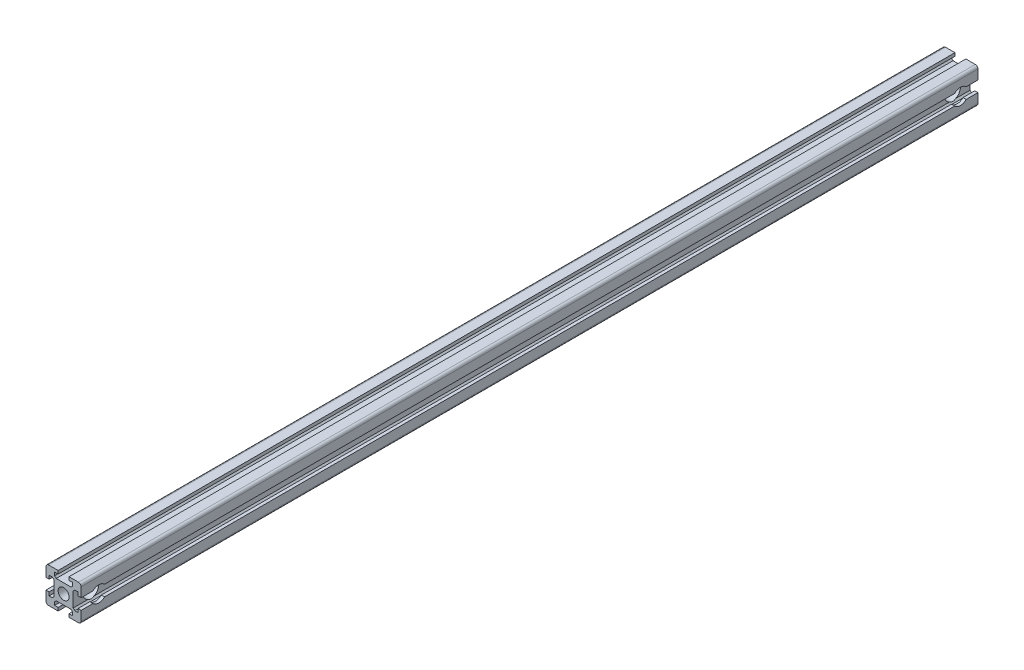
SolidWorks part; units mm, degrees
material "6061 Alloy"
ref_plane "Front Plane" through (0, 0, 0) normal (0, 0, 1) x (1, 0, 0)
ref_plane "Top Plane" through (0, 0, 0) normal (0, 1, 0) x (1, 0, 0)
ref_plane "Right Plane" through (0, 0, 0) normal (1, 0, 0) x (0, 0, -1)
sketch "Sketch1" plane through (0, 0, 0) normal (0, 0, 1) x (1, 0, 0)
  line L0 (-10, 3.1) -> (-8.2, 3.1)
  line L1 (-8.5, 10) -> (-3.1, 10) construction
  line L2 (-10, 8.5) -> (-10, 3.1) construction
  line L3 (-10, -3.1) -> (-10, -8.5) construction
  line L4 (-8.5, -10) -> (-3.1, -10) construction
  line L5 (-10, -3.1) -> (-10, -8.5)
  line L6 (-8.5, -10) -> (-3.1, -10)
  line L7 (-8.2, 3.1) -> (-8.2, 5.1)
  line L8 (-8.2, 5.1) -> (-6.4, 5.1)
  line L9 (-10, -3.1) -> (-8.2, -3.1)
  line L10 (-8.2, -3.1) -> (-8.2, -5.1)
  line L11 (-8.2, -5.1) -> (-6.4, -5.1)
  line L13 (-6.4, 5.1) -> (-5.4929, 4.1929)
  line L14 (-5.4929, 4.1929) -> (-5.4929, -4.1929)
  line L15 (-6.4, -5.1) -> (-5.4929, -4.1929)
  line L16 (-3.1, 10) -> (-3.1, 8.2)
  line L17 (-3.1, 8.2) -> (-5.1, 8.2)
  line L19 (-5.1, 8.2) -> (-5.1, 6.4)
  line L20 (-5.1, 6.4) -> (-4.1929, 5.4929)
  line L21 (-4.1929, 5.4929) -> (4.1929, 5.4929)
  line L22 (4.1929, 5.4929) -> (5.1, 6.4)
  line L23 (5.1, 6.4) -> (5.1, 8.2)
  line L24 (5.1, 8.2) -> (3.1, 8.2)
  line L25 (3.1, 8.2) -> (3.1, 10)
  line L26 (-3.1, -10) -> (-3.1, -8.2)
  line L27 (-3.1, -8.2) -> (-5.1, -8.2)
  line L28 (-5.1, -8.2) -> (-5.1, -6.4)
  line L29 (-5.1, -6.4) -> (-4.1929, -5.4929)
  line L30 (-4.1929, -5.4929) -> (4.1929, -5.4929)
  line L31 (4.1929, -5.4929) -> (5.1, -6.4)
  line L32 (5.1, -6.4) -> (5.1, -8.2)
  line L33 (5.1, -8.2) -> (3.1, -8.2)
  line L34 (3.1, -8.2) -> (3.1, -10)
  line L35 (3.1, -10) -> (8.5, -10)
  line L36 (10, -8.5) -> (10, -3.1)
  line L37 (10, -3.1) -> (8.2, -3.1)
  line L38 (8.2, -3.1) -> (8.2, -5.1)
  line L39 (8.2, -5.1) -> (6.4, -5.1)
  line L40 (6.4, -5.1) -> (5.4929, -4.1929)
  line L41 (5.4929, -4.1929) -> (5.4929, 4.1929)
  line L42 (5.4929, 4.1929) -> (6.4, 5.1)
  line L43 (6.4, 5.1) -> (8.2, 5.1)
  line L44 (8.2, 5.1) -> (8.2, 3.1)
  line L45 (8.2, 3.1) -> (10, 3.1)
  line L46 (10, 3.1) -> (10, 8.5)
  line L47 (8.5, 10) -> (3.1, 10)
  line L48 (-3.1, 10) -> (-8.5, 10)
  line L49 (-10, 8.5) -> (-10, 3.1)
  arc A0 (-8.5, 10) -> (-10, 8.5) centre (-8.5, 8.5) ccw
  arc A1 (-10, -8.5) -> (-8.5, -10) centre (-8.5, -8.5) ccw construction
  arc A2 (8.5, -10) -> (10, -8.5) centre (8.5, -8.5) ccw
  arc A3 (8.5, 10) -> (10, 8.5) centre (8.5, 8.5) cw
  arc A4 (-8.5, -10) -> (-10, -8.5) centre (-8.5, -8.5) cw
  circle A6 centre (0, 0) radius 3.1
  point P0 (0, 0)
  point P44 (-5.2, -3.4858)
  point P47 (-5.2, 3.4858)
  dimension "D3" = 5.4929
  dimension "D5" = 1.5
  dimension "D1" = 6.2
  dimension "D2" = 5.4929
  dimension "D4" = 1.5
  dimension "D6" = 1.5
extrude "Boss-Extrude1" add sketch "Sketch1" along normal blind 510
sketch "Sketch3" plane through (5.4929, 0, 0) normal (1, 0, 0) x (0, 0, -1)
  line L0 (0, -4.1929) -> (0, 4.1929) construction
  line L1 (-510, -10) -> (0, -10) construction
  line L2 (-510, -4.1929) -> (-510, 4.1929) construction
  circle A0 centre (-10, 0) radius 4.5
  circle A1 centre (-500, 0) radius 4.5
  point P4 (0, 0)
  dimension "D1" = 10
  dimension "D2" = 10
  dimension "D3" = 10
  dimension "D4" = 9
extrude "Cut-Extrude2" cut sketch "Sketch3" against normal blind 11 and the other way through all
